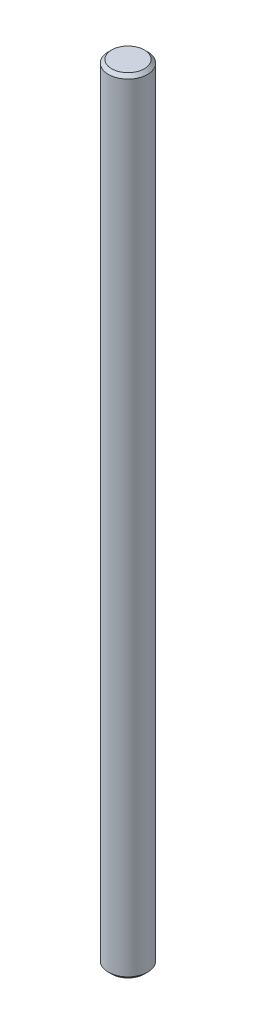
SolidWorks part; units mm, degrees
material "Acier non allié"
ref_plane "Plan de face" through (0, 0, 0) normal (0, 0, 1) x (1, 0, 0)
ref_plane "Plan de dessus" through (0, 0, 0) normal (0, 1, 0) x (1, 0, 0)
ref_plane "Plan de droite" through (0, 0, 0) normal (1, 0, 0) x (0, 0, -1)
sketch "Sketch1" plane through (0, 0, 0) normal (0, 1, 0) x (1, 0, 0)
  circle A0 centre (0, 0.0104) radius 6
  dimension "D1" = 12
extrude "Extrude1" add sketch "Sketch1" along normal blind 240
chamfer "Chamfer1" distance 1 angle 45 2 edges at (0, 0, 5.9896) (0, 240, 5.9896)
